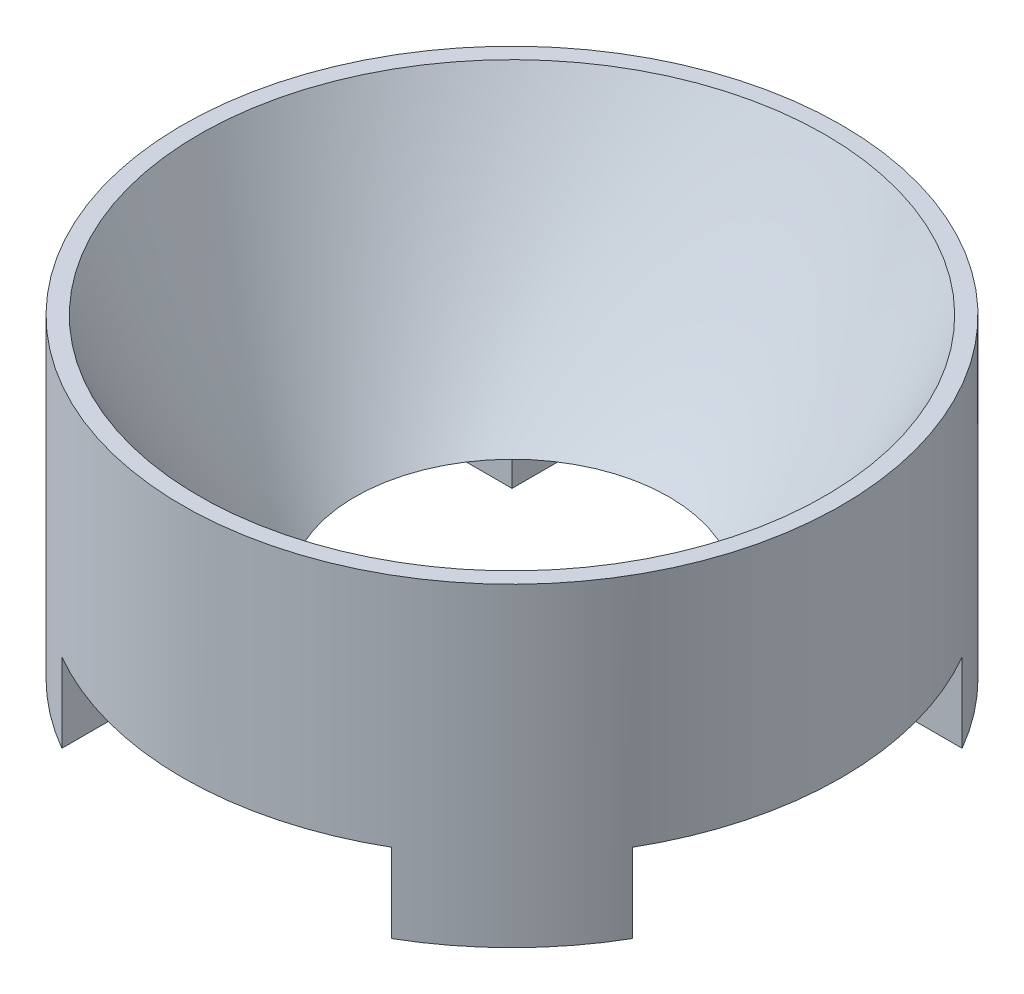
SolidWorks part; units mm, degrees
material "Brass"
ref_plane "Front Plane" through (0, 0, 0) normal (0, 0, 1) x (1, 0, 0)
ref_plane "Top Plane" through (0, 0, 0) normal (0, 1, 0) x (1, 0, 0)
ref_plane "Right Plane" through (0, 0, 0) normal (1, 0, 0) x (0, 0, -1)
sketch "Sketch1" plane through (0, 0, 0) normal (0, 0, 1) x (1, 0, 0)
  line L0 (0, -656.2992) -> (0, 32158.6614) construction
  line L1 (-1000, 0) -> (49000, 0) construction
  line L2 (6.0326, 6.0653) -> (6.35, 6.0653)
  line L3 (3, 0) -> (3, 1.5)
  line L4 (3, -997.4439) -> (3, 49002.5561) construction
  line L5 (3, 0) -> (6.35, 0)
  line L6 (6.35, 0) -> (6.35, 6.0653)
  spline S0 degree 2 poles (0, 0) (3.175, 0) (6.35, 6.7204) knots 0 0 0 1 1 1 construction
  spline S1 degree 2 poles (0, 0) (3.175, 0) (6.35, 6.7204) knots 0 0 0 1 1 1 construction
  spline S2 degree 2 poles (3, 1.5) (4.4648, 3.2199) (6.0326, 6.0653) knots 0 0 0 1 1 1 construction
  spline S3 degree 2 poles (3, 1.5) (4.5163, 3.0163) (6.0326, 6.0653) knots 0.189542 0.189542 0.189542 0.293296 0.293296 0.293296
  dimension "D1" = 12.7
  dimension "D2" = 3
revolve "Revolve1" add sketch "Sketch1" angle 360 about L0
sketch "Sketch2" plane through (0, 0, 0) normal (0, -1, 0) x (1, 0, 0)
  line L1 (-3.175, 13.6828) -> (3.175, 13.6828)
  line L2 (-3.175, 13.6828) -> (-3.175, 3.175)
  line L3 (-3.175, -13.6828) -> (3.175, -13.6828)
  line L4 (3.175, 13.6828) -> (3.175, 3.175)
  line L5 (-3.175, 13.6828) -> (3.175, -13.6828) construction
  line L6 (-3.175, -13.6828) -> (3.175, 13.6828) construction
  line L7 (-13.6828, 3.175) -> (-3.175, 3.175)
  line L8 (-13.6828, 3.175) -> (-13.6828, -3.175)
  line L9 (-13.6828, -3.175) -> (-3.175, -3.175)
  line L10 (13.6828, 3.175) -> (13.6828, -3.175)
  line L11 (-13.6828, 3.175) -> (13.6828, -3.175) construction
  line L12 (-13.6828, -3.175) -> (13.6828, 3.175) construction
  line L14 (-3.175, -3.175) -> (-3.175, -13.6828)
  line L16 (3.175, -3.175) -> (13.6828, -3.175)
  line L17 (3.175, -3.175) -> (3.175, -13.6828)
  line L19 (3.175, 3.175) -> (13.6828, 3.175)
  point P0 (0, 0)
  point P6 (0, 0)
  dimension "D1" = 6.35
extrude "Cut-Extrude1" cut sketch "Sketch2" against normal blind 1.524
